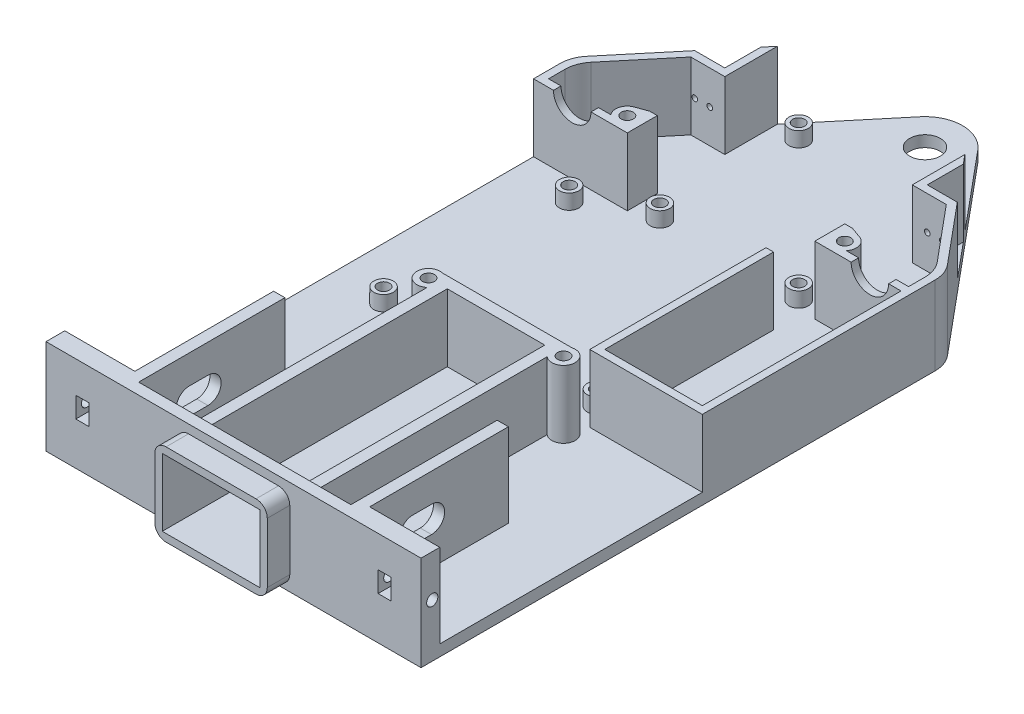
SolidWorks part; units mm, degrees
ref_plane "Front Plane" through (0, 0, 0) normal (0, 0, 1) x (1, 0, 0)
ref_plane "Top Plane" through (0, 0, 0) normal (0, 1, 0) x (1, 0, 0)
ref_plane "Right Plane" through (0, 0, 0) normal (1, 0, 0) x (0, 0, -1)
sketch "Sketch1" plane through (0, 0, 0) normal (0, 1, 0) x (1, 0, 0)
  line L1 (50, 70) -> (-50, 70)
  line L2 (50, 70) -> (50, -70)
  line L3 (50, -70) -> (-50, -70)
  line L4 (-50, 70) -> (-50, -70)
  line L5 (50, 70) -> (-50, -70) construction
  line L6 (50, -70) -> (-50, 70) construction
  point P0 (0, 0)
  dimension "D1" = 100
  dimension "D2" = 140
extrude "Boss-Extrude1" add sketch "Sketch1" along normal blind 3
sketch "Sketch2" plane through (0, 3, 0) normal (0, 1, 0) x (1, 0, 0)
  line L0 (-50, 70) -> (-50, -70) construction
  line L1 (-50, -70) -> (50, -70) construction
  line L2 (-50, -65) -> (-50, -70)
  line L3 (-50, -70) -> (50, -70) construction
  line L4 (-50, -70) -> (-28.3, -70)
  line L5 (-28.3, -70) -> (-28.3, -28)
  line L6 (-28.3, -28) -> (-31.3, -28)
  line L7 (-31.3, -28) -> (-31.3, -65)
  line L8 (-31.3, -65) -> (-50, -65)
  line L9 (-50, -65) -> (-50, -70) construction
  dimension "D1" = 5
  dimension "D2" = 18.7
  dimension "D3" = 37
  dimension "D4" = 3
extrude "Boss-Extrude2" add sketch "Sketch2" along normal blind 22.3
sketch "Sketch4" plane through (0, 0, 65) normal (0, 0, -1) x (-1, 0, 0)
  line L0 (40.3, 3) -> (40.3, 25.3) construction
  line L2 (38.55, 11.4) -> (42.05, 11.4)
  line L3 (38.55, 11.4) -> (38.55, 16.9)
  line L4 (31.3, 3) -> (50, 3)
  line L5 (50, 3) -> (50, 25.3)
  line L6 (50, 25.3) -> (31.3, 25.3)
  line L7 (31.3, 25.3) -> (31.3, 3)
  line L8 (31.3, 3) -> (50, 3) construction
  line L9 (50, 3) -> (50, 25.3) construction
  line L10 (50, 25.3) -> (31.3, 25.3) construction
  line L11 (31.3, 25.3) -> (31.3, 3) construction
  line L12 (38.55, 16.9) -> (42.05, 16.9)
  line L13 (42.05, 11.4) -> (42.05, 16.9)
  line L14 (38.55, 11.4) -> (42.05, 16.9) construction
  line L15 (38.55, 16.9) -> (42.05, 11.4) construction
  point P6 (40.3, 14.15)
  dimension "D2" = 3.5
  dimension "D3" = 5.5
  dimension "D4" = 9
  dimension "D1" = 0
extrude "Cut-Extrude2" cut sketch "Sketch4" against normal up to next (5 mm away)
sketch "Sketch3" plane through (-31.3, 0, 0) normal (-1, 0, 0) x (0, 0, 1)
  line L0 (28, 25.3) -> (65, 25.3) construction
  line L1 (28, 3) -> (65, 3) construction
  line L2 (28, 25.3) -> (65, 25.3) construction
  line L3 (28, 3) -> (65, 3) construction
  line L4 (75.1807, 14.15) -> (-7.7773, 14.15) construction
  line L5 (65, 25.3) -> (65, 3) construction
  line L6 (53.5, 14.15) -> (48.5, 14.15) construction
  line L7 (65, 25.3) -> (65, 3) construction
  line L8 (53.5, 10.65) -> (48.5, 10.65)
  line L9 (53.5, 17.65) -> (48.5, 17.65)
  circle A0 centre (53.5, 14.15) radius 3.5 construction
  circle A1 centre (67, 14.15) radius 1.5
  arc A2 (53.5, 10.65) -> (53.5, 17.65) centre (53.5, 14.15) ccw
  arc A3 (48.5, 17.65) -> (48.5, 10.65) centre (48.5, 14.15) ccw
  point P14 (51, 14.15)
  dimension "D1" = 7
  dimension "D3" = 2
  dimension "D4" = 3
  dimension "D2" = 11.5
  dimension "D5" = 7
  dimension "D6" = 5
extrude "Cut-Extrude1" cut sketch "Sketch3" against normal up to surface (3 mm away) and the other way through all up to face at (-28.3, 14.15, 49)
mirror "Mirror1" about plane through (0, 0, 0) normal (1, 0, 0) of "Cut-Extrude1", "Boss-Extrude2", "Cut-Extrude2"
sketch "Sketch5" plane through (0, 3, 0) normal (0, 1, 0) x (1, 0, 0)
  line L0 (-28.3, -70) -> (28.3, -70) construction
  line L1 (-28.3, -70) -> (28.3, -70) construction
  line L2 (0, 66.1657) -> (0, -98.9491) construction
  line L3 (13, -70) -> (16, -70)
  line L4 (16, -70) -> (16, 3)
  line L5 (16, 3) -> (-16, 3)
  line L6 (-16, 3) -> (-16, -70)
  line L7 (-16, -70) -> (-13, -70)
  line L8 (-13, -70) -> (-13, 0)
  line L9 (-13, 0) -> (13, 0)
  line L10 (13, 0) -> (13, -70)
  dimension "D1" = 3
  dimension "D2" = 3
  dimension "D3" = 70
  dimension "D4" = 26
extrude "Boss-Extrude3" add sketch "Sketch5" along normal blind 18
sketch "Sketch6" plane through (0, 0, 70) normal (0, 0, 1) x (1, 0, 0)
  line L0 (28.3, 25.3) -> (28.3, 3) construction
  line L1 (16, 3) -> (28.3, 3) construction
  line L2 (16, 21) -> (16, 3) construction
  line L3 (13, 21) -> (16, 21) construction
  line L4 (-16, 21) -> (-13, 21) construction
  line L5 (-16, 21) -> (-16, 3) construction
  line L6 (-28.3, 3) -> (-16, 3) construction
  line L7 (-28.3, 25.3) -> (-28.3, 3) construction
  line L8 (28.3, 25.3) -> (28.3, 3)
  line L9 (16, 3) -> (28.3, 3)
  line L10 (16, 21) -> (16, 3)
  line L11 (13, 21) -> (16, 21)
  line L12 (-16, 21) -> (-13, 21)
  line L13 (-16, 21) -> (-16, 3)
  line L14 (-28.3, 3) -> (-16, 3)
  line L15 (-28.3, 25.3) -> (-28.3, 3)
  line L16 (28.3, 25.3) -> (-28.3, 25.3)
  line L17 (-13, 21) -> (13, 21)
extrude "Boss-Extrude4" add sketch "Sketch6" against normal blind 3
sketch "Sketch7" plane through (0, 0, 70) normal (0, 0, 1) x (1, 0, 0)
  line L0 (-13, 21) -> (-13, 3) construction
  line L1 (-13, 21) -> (13, 21) construction
  line L2 (13, 21) -> (13, 3) construction
  line L3 (-13, 3) -> (13, 3) construction
  line L4 (-13, 21) -> (-13, 3)
  line L5 (-13, 21) -> (13, 21)
  line L6 (13, 21) -> (13, 3)
  line L7 (-13, 3) -> (13, 3)
  line L8 (-12, 23) -> (12, 23)
  line L9 (15, 20) -> (15, 4)
  line L10 (-12, 1) -> (12, 1)
  line L11 (-15, 20) -> (-15, 4)
  line L12 (-15, 1) -> (15, 1) construction
  line L13 (-15, 23) -> (-15, 1) construction
  line L14 (15, 23) -> (15, 1) construction
  line L15 (-15, 23) -> (15, 23) construction
  arc A0 (-12, 1) -> (-15, 4) centre (-12, 4) cw
  arc A1 (15, 4) -> (12, 1) centre (12, 4) cw
  arc A2 (12, 23) -> (15, 20) centre (12, 20) cw
  arc A3 (-12, 23) -> (-15, 20) centre (-12, 20) ccw
  dimension "D2" = 3
  dimension "D1" = 2
extrude "Boss-Extrude5" add sketch "Sketch7" along normal blind 6
sketch "Sketch10" plane through (0, 3, 0) normal (0, 1, 0) x (1, 0, 0)
  line L0 (50, 70) -> (-50, 70) construction
  line L1 (50, 70) -> (-50, 70)
  line L2 (50, 70) -> (0, 130)
  line L3 (0, 130) -> (-50, 70)
  dimension "D1" = 60
extrude "Boss-Extrude8" add sketch "Sketch10" against normal up to surface (3 mm away) up to face at (0, 0, 0)
sketch "Sketch9" plane through (0, 3, 0) normal (0, 1, 0) x (1, 0, 0)
  line L0 (-65.8457, 6) -> (67.0276, 6) construction
  line L1 (16, 3) -> (-16, 3) construction
  line L2 (16.1, 64.5341) -> (16.1, 4.2599) construction
  line L3 (68.4136, 54.2) -> (-72.6094, 54.2) construction
  line L4 (-50, 70) -> (-50, -65) construction
  line L5 (-72.6094, 62.2) -> (68.4136, 62.2) construction
  line L7 (-72.6094, 99.2) -> (68.513, 99.2) construction
  line L8 (-18.5, 62.2) -> (-18.5, 99.2) construction
  line L9 (18.5, 62.2) -> (18.5, 99.2) construction
  line L10 (0, 0) -> (0, 140.9733) construction
  circle A0 centre (-36, 6) radius 1.6
  circle A1 centre (16.1, 38.7) radius 1.6
  circle A2 centre (16.1, 10.8) radius 1.6
  circle A3 centre (-34.7, 54.2) radius 1.6
  circle A4 centre (-34.7, 54.2) radius 2.6
  circle A5 centre (-36, 6) radius 2.6
  circle A6 centre (16.1, 10.8) radius 2.6
  circle A7 centre (16.1, 38.7) radius 2.6
  circle A8 centre (-18.5, 62.2) radius 1.6
  circle A9 centre (18.5, 62.2) radius 1.6
  circle A10 centre (-18.5, 99.2) radius 1.6
  circle A11 centre (18.5, 99.2) radius 1.6
  circle A12 centre (-18.5, 62.2) radius 2.6
  circle A13 centre (-18.5, 99.2) radius 2.6
  circle A14 centre (18.5, 99.2) radius 2.6
  circle A15 centre (18.5, 62.2) radius 2.6
  dimension "D2" = 27.9
  dimension "D3" = 48.2
  dimension "D4" = 3.2
  dimension "D11" = 37
  dimension "D13" = 3.2
  dimension "D1" = 3
  dimension "D5" = 52.1
  dimension "D6" = 50.8
  dimension "D7" = 14
  dimension "D8" = 15.5
  dimension "D10" = 8
  dimension "D12" = 37
  dimension "D14" = 1
  dimension "D9" = 1
extrude "Boss-Extrude7" add sketch "Sketch9" along normal blind 4
sketch "Sketch11" plane through (0, 3, 0) normal (0, 1, 0) x (1, 0, 0)
  line L0 (50, -65) -> (50, 70) construction
  line L1 (50, 5) -> (50, 70)
  line L2 (50, 5) -> (20, 5)
  line L3 (31.3, -65) -> (50, -65) construction
  line L4 (20, 5) -> (20, 52)
  line L5 (20, 52) -> (22, 52)
  line L6 (22, 52) -> (22, 7)
  line L7 (22, 7) -> (48, 7)
  line L8 (48, 7) -> (48, 60)
  line L10 (-50, 70) -> (-50, -65) construction
  line L11 (-50, 70) -> (-50, 60)
  line L12 (0, 130) -> (-50, 70) construction
  line L13 (-25, 100) -> (-27, 97.6)
  line L14 (50, 70) -> (0, 130) construction
  line L15 (50, 70) -> (35, 88)
  line L16 (25, 100) -> (25, 96.8759)
  line L17 (-25, 100) -> (-25, 96.8759)
  line L18 (0, -101.8169) -> (0, 159.6261) construction
  line L19 (-50, 60) -> (-25, 60)
  line L20 (25, 60) -> (48, 60)
  line L21 (-48, 62) -> (-27, 62)
  line L22 (-27, 68) -> (-27, 62)
  line L23 (-34.0633, 86) -> (-48, 69.2759)
  line L24 (-48, 69.2759) -> (-48, 62)
  line L25 (27, 62) -> (48, 62)
  line L26 (48, 62) -> (48, 62)
  line L27 (48, 62) -> (48, 62)
  line L28 (48, 62) -> (48, 62)
  line L29 (48, 62) -> (48, 62)
  line L30 (48, 62) -> (48, 62)
  line L31 (48, 62) -> (48, 62)
  line L32 (48, 62) -> (48, 69.2759)
  line L33 (48, 69.2759) -> (34.0633, 86)
  line L34 (27, 68) -> (27, 62)
  line L35 (-27, 94.4759) -> (-48, 69.2759) construction
  line L36 (48, 69.2759) -> (27, 94.4759) construction
  line L37 (25, 68) -> (27, 68)
  line L38 (-25, 68) -> (-27, 68)
  line L39 (-25, 68) -> (-25, 60)
  line L40 (-27, 94.4759) -> (-27, 68) construction
  line L41 (-27, 94.4759) -> (-27, 62) construction
  line L42 (25, 68) -> (25, 60)
  line L43 (-25, 96.8759) -> (-25, 68) construction
  line L44 (-25, 100) -> (-25, 60) construction
  line L45 (-27, 97.6) -> (-27, 88)
  line L46 (25, 96.8759) -> (25, 68) construction
  line L47 (25, 100) -> (25, 60) construction
  line L48 (27, 94.4759) -> (27, 68) construction
  line L49 (27, 94.4759) -> (27, 62) construction
  line L50 (-27, 86) -> (-25, 86)
  line L51 (-25, 86) -> (-25, 96.8759)
  line L52 (25, 96.8759) -> (25, 86)
  line L53 (25, 86) -> (27, 86)
  line L54 (27, 88) -> (27, 97.6)
  line L55 (27, 94.4759) -> (25, 96.8759) construction
  line L56 (-25, 96.8759) -> (-27, 94.4759) construction
  line L57 (-27, 86) -> (-34.0633, 86)
  line L58 (-27, 88) -> (-35, 88)
  line L59 (-27, 94.4759) -> (-32.3966, 88) construction
  line L60 (-35, 88) -> (-50, 70)
  line L61 (-32.3966, 88) -> (-34.0633, 86) construction
  line L62 (-27, 97.6) -> (-35, 88) construction
  line L63 (-25, 100) -> (-50, 70) construction
  line L64 (-27, 88) -> (-27, 86) construction
  line L65 (27, 86) -> (34.0633, 86)
  line L66 (27, 88) -> (35, 88)
  line L67 (27, 97.6) -> (25, 100)
  line L68 (32.3966, 88) -> (27, 94.4759) construction
  line L69 (35, 88) -> (27, 97.6) construction
  line L70 (50, 70) -> (25, 100) construction
  line L71 (27, 86) -> (27, 88) construction
  line L72 (34.0633, 86) -> (32.3966, 88) construction
  dimension "D1" = 70
  dimension "D2" = 45
  dimension "D3" = 2
  dimension "D4" = 50
  dimension "D5" = 10
  dimension "D6" = 2
  dimension "D7" = 2
  dimension "D9" = 26
  dimension "D10" = 8
  dimension "D11" = 18
  dimension "D12" = 2
  dimension "D13" = 2
  dimension "D8" = 2
extrude "Boss-Extrude9" add sketch "Sketch11" along normal blind 18
sketch "Sketch13" plane through (0, 3, 0) normal (0, 1, 0) x (1, 0, 0)
  line L0 (-59.1741, 0) -> (85.9739, 0) construction
  line L1 (65.4383, 64) -> (-66.6672, 64) construction
  line L2 (0, -95.2633) -> (0, 169.9815) construction
  line L3 (27, 62) -> (48, 62) construction
  line L4 (27, 68) -> (27, 62) construction
  line L5 (16, -67) -> (16, 3) construction
  line L6 (16, 2.3685) -> (16, 3)
  line L7 (16, 3) -> (17.219, 3)
  line L8 (27, 62) -> (27, 68) construction
  line L9 (27, 62) -> (27, 64) construction
  line L10 (27, 66.3685) -> (27, 68)
  line L11 (27, 64) -> (27, 66.3685) construction
  line L12 (27, 68) -> (30.0375, 66.9212)
  circle A0 centre (29, 64) radius 1.6
  circle A1 centre (18, 0) radius 1.6
  arc A2 (27, 66.3685) -> (30.0375, 66.9212) centre (29, 64) ccw
  arc A3 (16, 2.3685) -> (17.219, 3) centre (18, 0) ccw
  arc A5 (17.219, 3) -> (16, 2.3685) centre (18, 0) ccw construction
  circle A6 centre (18, 0) radius 3.1 construction
  arc A7 (30.0375, 66.9212) -> (27, 66.3685) centre (29, 64) ccw construction
  circle A8 centre (29, 64) radius 3.1 construction
  point P23 (21.1, 0)
  point P29 (32.1, 64)
  dimension "D2" = 2
  dimension "D3" = 2
  dimension "D4" = 3.2
  dimension "D1" = 2
  dimension "D5" = 1.5
extrude "Boss-Extrude10" add sketch "Sketch13" along normal blind 18
sketch "Sketch12" plane through (0, 3, 0) normal (0, 1, 0) x (1, 0, 0)
  line L0 (0, -129.5183) -> (0, 162.2572) construction
  line L1 (25, 100) -> (0, 130) construction
  line L2 (0, 130) -> (-25, 100) construction
  line L3 (7.6822, 120.7813) -> (0, 130)
  line L4 (0, 130) -> (-7.6822, 120.7813)
  circle A0 centre (0, 114.3795) radius 4.1
  arc A1 (7.6822, 120.7813) -> (-7.6822, 120.7813) centre (0, 114.3795) ccw
  dimension "D1" = 8.2
  dimension "D2" = 20
extrude "Cut-Extrude3" cut sketch "Sketch12" against normal up to next
sketch "Sketch14" plane through (0, 0, -88) normal (0, 0, -1) x (-1, 0, 0)
  line L0 (-35, 3) -> (-27, 3) construction
  line L1 (-35, 21) -> (-27, 21) construction
  line L2 (-35, 3) -> (-27, 3) construction
  line L3 (-35, 21) -> (-27, 21) construction
  line L4 (-31, 21) -> (-31, 3) construction
  line L5 (-27, 12) -> (-35, 12) construction
  line L6 (-35, 21) -> (-35, 3) construction
  line L7 (-27, 21) -> (-27, 3) construction
  circle A0 centre (-29, 12) radius 0.75
  circle A1 centre (-33, 12) radius 0.75
  dimension "D1" = 2
  dimension "D2" = 1.5
extrude "Cut-Extrude4" cut sketch "Sketch14" against normal up to next (2 mm away)
sketch "Sketch15" plane through (0, 0, -62) normal (0, 0, -1) x (-1, 0, 0)
  line L0 (-48, 21) -> (-31.3685, 21) construction
  line L1 (-48, 21) -> (-31.3685, 21)
  line L2 (-39.6843, 21) -> (-39.6843, 16) construction
  line L3 (-44.6843, 21) -> (-34.6843, 21)
  arc A0 (-44.6843, 21) -> (-34.6843, 21) centre (-39.6843, 21) ccw
  arc A1 (-34.6843, 21) -> (-44.6843, 21) centre (-39.6843, 21) ccw construction
  dimension "D1" = 5
extrude "Cut-Extrude5" cut sketch "Sketch15" against normal up to next (2 mm away) contours A0 L3
fillet "Fillet2" radius 8 4 edges at (50, 10.5, -70) (-50, 10.5, -70) (-48, 12, -69.2759) (48, 12, -69.2759)
mirror "Mirror2" about plane through (0, 0, 0) normal (1, 0, 0) of "Cut-Extrude5", "Boss-Extrude10", "Cut-Extrude4"
